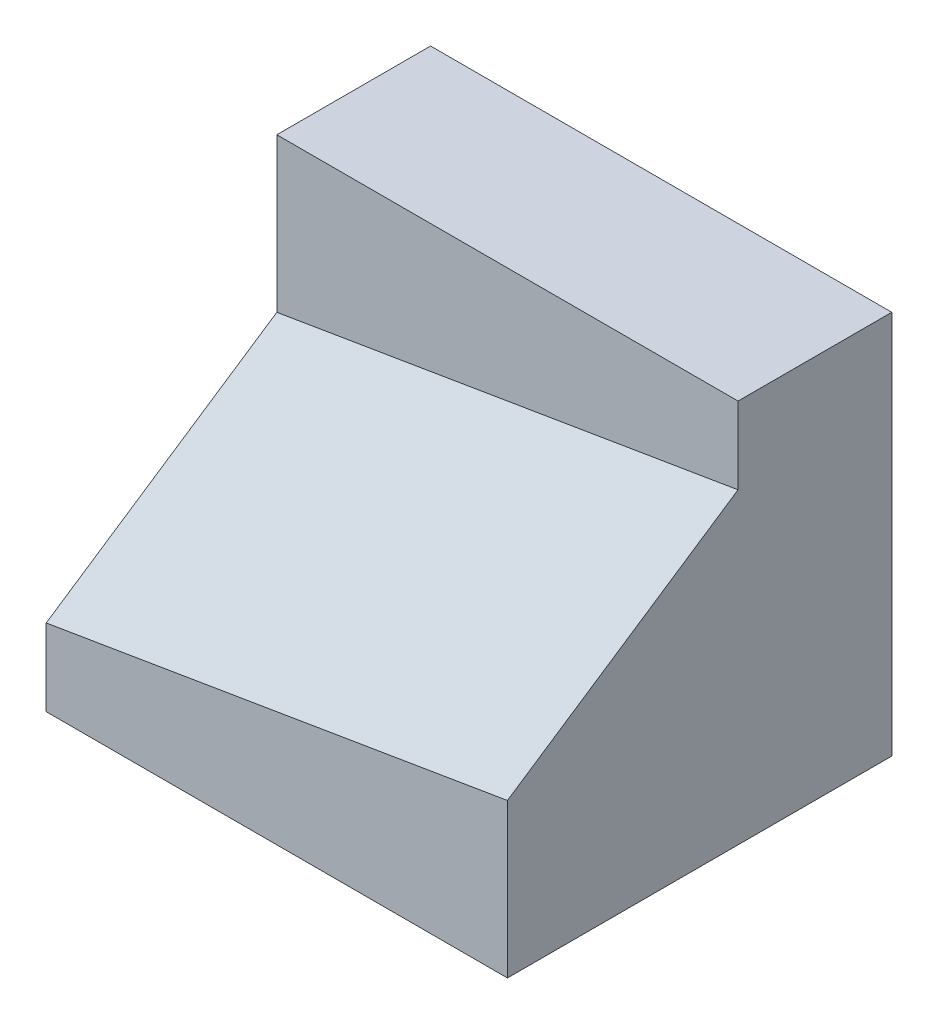
SolidWorks part; units mm, degrees
ref_plane "Front Plane" through (0, 0, 0) normal (0, 0, 1) x (1, 0, 0)
ref_plane "Top Plane" through (0, 0, 0) normal (0, 1, 0) x (1, 0, 0)
ref_plane "Right Plane" through (0, 0, 0) normal (1, 0, 0) x (0, 0, -1)
sketch "Sketch1" plane through (0, 0, 0) normal (0, 0, 1) x (1, 0, 0)
  line L0 (0, 0) -> (-30, 0)
  line L1 (-30, 0) -> (-30, 25)
  line L2 (-30, 25) -> (0, 25)
  line L3 (0, 25) -> (0, 0)
  dimension "D1" = 25
  dimension "D2" = 30
extrude "Boss-Extrude1" add sketch "Sketch1" along normal blind 25
sketch3d "3DSketch1"
  line L0 (0, 25, 25) -> (0, 25, 0) construction
  line L1 (-30, 25, 25) -> (-30, 0, 25) construction
  line L2 (-30, 25, 25) -> (-30, 25, 0) construction
  line L3 (-30, 15, 10) -> (0, 20, 10)
  line L4 (0, 20, 10) -> (0, 10, 25)
  line L5 (0, 0, 25) -> (0, 25, 25) construction
  line L7 (-30, 15, 10) -> (-30, 5, 25)
  line L8 (0, 10, 25) -> (-30, 5, 25)
  point P0 (0, 15, 10)
  point P1 (0, 10, 25)
  point P4 (-30, 5, 25)
  point P6 (-30, 15, 10)
  dimension "D1" = 10
  dimension "D2" = 15
  dimension "D3" = 5
  dimension "D4" = 15
  dimension "D5" = 10
  dimension "D6" = 10
extrude "Cut-Extrude4" cut sketch "3DSketch1" along direction (0, -1, 0) on the side against the normal blind 25
